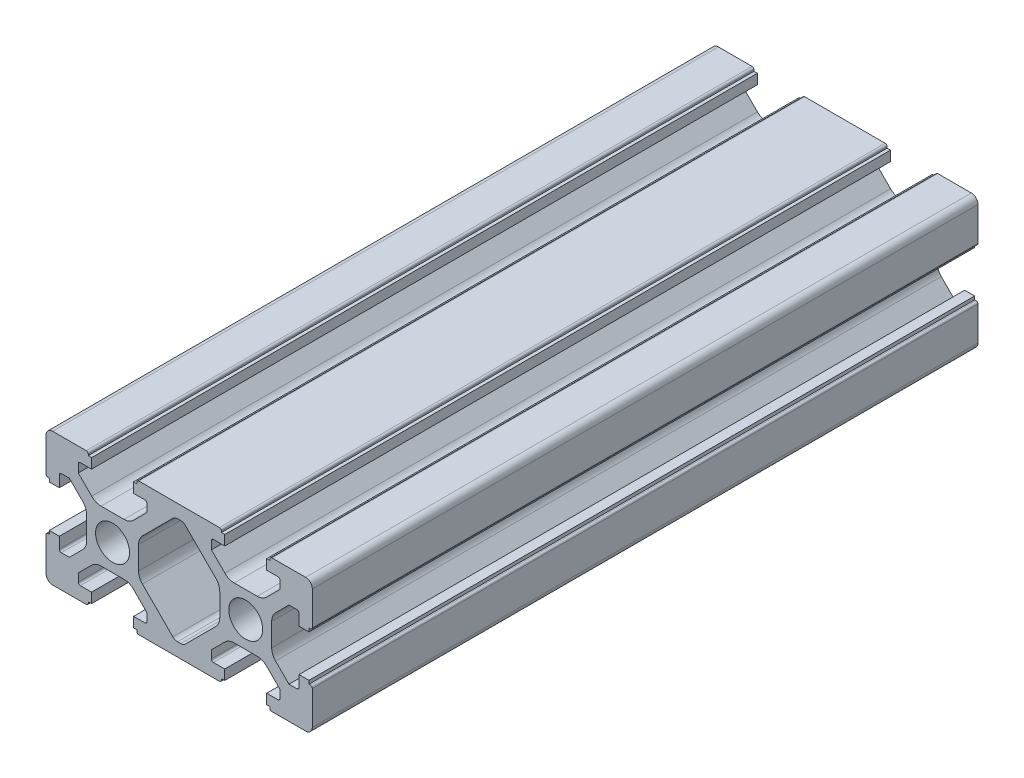
SolidWorks part; units mm, degrees
ref_plane "Front" through (0, 0, 0) normal (0, 0, 1) x (1, 0, 0)
ref_plane "Top" through (0, 0, 0) normal (0, 1, 0) x (1, 0, 0)
ref_plane "Right" through (0, 0, 0) normal (1, 0, 0) x (0, 0, -1)
sketch "草图1" plane through (0, 0, 0) normal (0, 0, 1) x (1, 0, 0)
  line L0 (-23.1654, -6.3888) -> (-23.1654, -1.3388)
  line L1 (-22.8654, -1.0388) -> (-22.6654, -1.0388)
  line L2 (-22.6654, -1.0388) -> (-22.6654, -0.5388)
  line L3 (-22.6654, -0.5388) -> (-21.1654, -0.5388)
  line L4 (-21.1654, -0.5388) -> (-21.1654, -2.2388)
  line L5 (-17.0654, 0.8896) -> (-17.0654, 4.3328)
  line L6 (-21.1654, 5.7612) -> (-21.1654, 7.4612)
  line L7 (-22.6654, 5.7612) -> (-21.1654, 5.7612)
  line L8 (-22.6654, 6.2612) -> (-22.6654, 5.7612)
  line L9 (-22.8654, 6.2612) -> (-22.6654, 6.2612)
  line L10 (-23.1654, 11.6112) -> (-23.1654, 6.5612)
  line L11 (-20.8654, 7.7612) -> (-19.6654, 7.7612)
  line L12 (-19.6654, 7.7612) -> (-17.6512, 5.747)
  line L13 (-19.6654, -2.5388) -> (-17.6512, -0.5246)
  line L14 (-20.8654, -2.5388) -> (-19.6654, -2.5388)
  line L15 (-8.0154, 10.3112) -> (-8.0154, 9.1112)
  line L16 (-8.0154, 9.1112) -> (-10.0296, 7.097)
  line L17 (-18.3154, 9.1112) -> (-16.3012, 7.097)
  line L18 (-18.3154, 10.3112) -> (-18.3154, 9.1112)
  line L19 (-22.1654, 12.6112) -> (-17.1154, 12.6112)
  line L20 (-16.8154, 12.3112) -> (-16.8154, 12.1112)
  line L21 (-16.8154, 12.1112) -> (-16.3154, 12.1112)
  line L22 (-16.3154, 12.1112) -> (-16.3154, 10.6112)
  line L23 (-16.3154, 10.6112) -> (-18.0154, 10.6112)
  line L24 (-11.4438, 6.5112) -> (-14.887, 6.5112)
  line L25 (-10.0154, 10.6112) -> (-8.3154, 10.6112)
  line L26 (-10.0154, 12.1112) -> (-10.0154, 10.6112)
  line L27 (-9.5154, 12.1112) -> (-10.0154, 12.1112)
  line L28 (-9.5154, 12.3112) -> (-9.5154, 12.1112)
  line L29 (-9.2654, 4.3328) -> (-9.2654, 0.8896)
  line L30 (-6.6654, 7.7612) -> (-8.6796, 5.747)
  line L31 (-18.3154, -5.0888) -> (-18.3154, -3.8888)
  line L32 (-18.3154, -3.8888) -> (-16.3012, -1.8746)
  line L33 (-8.0154, -3.8888) -> (-10.0296, -1.8746)
  line L34 (-8.0154, -5.0888) -> (-8.0154, -3.8888)
  line L35 (-3.1654, -7.3888) -> (-9.2154, -7.3888)
  line L36 (-9.5154, -7.0888) -> (-9.5154, -6.8888)
  line L37 (-9.5154, -6.8888) -> (-10.0154, -6.8888)
  line L38 (-10.0154, -6.8888) -> (-10.0154, -5.3888)
  line L39 (-10.0154, -5.3888) -> (-8.3154, -5.3888)
  line L40 (-14.887, -1.2888) -> (-11.4438, -1.2888)
  line L41 (-16.3154, -5.3888) -> (-18.0154, -5.3888)
  line L42 (-16.3154, -6.8888) -> (-16.3154, -5.3888)
  line L43 (-16.8154, -6.8888) -> (-16.3154, -6.8888)
  line L44 (-16.8154, -7.0888) -> (-16.8154, -6.8888)
  line L45 (-22.1654, -7.3888) -> (-17.1154, -7.3888)
  line L46 (2.9346, 0.8896) -> (2.9346, 4.3328)
  line L47 (0.3346, 7.7612) -> (2.3488, 5.747)
  line L48 (11.9846, 10.3112) -> (11.9846, 9.1112)
  line L49 (11.9846, 9.1112) -> (9.9704, 7.097)
  line L50 (1.6846, 9.1112) -> (3.6988, 7.097)
  line L51 (1.6846, 10.3112) -> (1.6846, 9.1112)
  line L52 (3.1846, 12.3112) -> (3.1846, 12.1112)
  line L53 (3.1846, 12.1112) -> (3.6846, 12.1112)
  line L54 (3.6846, 12.1112) -> (3.6846, 10.6112)
  line L55 (3.6846, 10.6112) -> (1.9846, 10.6112)
  line L56 (8.5562, 6.5112) -> (5.113, 6.5112)
  line L57 (9.9846, 10.6112) -> (11.6846, 10.6112)
  line L58 (9.9846, 12.1112) -> (9.9846, 10.6112)
  line L59 (10.4846, 12.1112) -> (9.9846, 12.1112)
  line L60 (10.4846, 12.3112) -> (10.4846, 12.1112)
  line L61 (15.8346, 12.6112) -> (10.7846, 12.6112)
  line L62 (16.8346, 11.6112) -> (16.8346, 6.5612)
  line L63 (16.5346, 6.2612) -> (16.3346, 6.2612)
  line L64 (16.3346, 6.2612) -> (16.3346, 5.7612)
  line L65 (16.3346, 5.7612) -> (14.8346, 5.7612)
  line L66 (14.8346, 5.7612) -> (14.8346, 7.4612)
  line L67 (10.7346, 4.3328) -> (10.7346, 0.8896)
  line L68 (14.8346, -0.5388) -> (14.8346, -2.2388)
  line L69 (16.3346, -0.5388) -> (14.8346, -0.5388)
  line L70 (16.3346, -1.0388) -> (16.3346, -0.5388)
  line L71 (16.5346, -1.0388) -> (16.3346, -1.0388)
  line L72 (16.8346, -6.3888) -> (16.8346, -1.3388)
  line L73 (14.5346, -2.5388) -> (13.3346, -2.5388)
  line L74 (13.3346, -2.5388) -> (11.3204, -0.5246)
  line L75 (13.3346, 7.7612) -> (11.3204, 5.747)
  line L76 (14.5346, 7.7612) -> (13.3346, 7.7612)
  line L77 (1.6846, -5.0888) -> (1.6846, -3.8888)
  line L78 (1.6846, -3.8888) -> (3.6988, -1.8746)
  line L79 (11.9846, -3.8888) -> (9.9704, -1.8746)
  line L80 (11.9846, -5.0888) -> (11.9846, -3.8888)
  line L81 (15.8346, -7.3888) -> (10.4846, -7.3888)
  line L82 (10.4846, -7.3888) -> (10.4846, -6.8888)
  line L83 (10.4846, -6.8888) -> (9.9846, -6.8888)
  line L84 (9.9846, -6.8888) -> (9.9846, -5.3888)
  line L85 (9.9846, -5.3888) -> (11.6846, -5.3888)
  line L86 (5.113, -1.2888) -> (8.5562, -1.2888)
  line L87 (3.6846, -5.3888) -> (1.9846, -5.3888)
  line L88 (3.6846, -6.8888) -> (3.6846, -5.3888)
  line L89 (3.1846, -6.8888) -> (3.6846, -6.8888)
  line L90 (3.1846, -7.0888) -> (3.1846, -6.8888)
  line L91 (-3.1654, -7.3888) -> (2.8846, -7.3888)
  line L92 (-6.6654, 7.7612) -> (-4.1083, 10.3183)
  line L93 (0.3346, 7.7612) -> (-2.2225, 10.3183)
  line L94 (-3.4012, 10.6112) -> (-2.9296, 10.6112)
  line L95 (-9.2154, 12.6112) -> (2.8846, 12.6112)
  line L96 (-3.4012, -5.3888) -> (-2.9296, -5.3888)
  line L97 (0.3346, -2.5388) -> (-2.2225, -5.0959)
  line L98 (-6.6654, -2.5388) -> (-4.1083, -5.0959)
  line L99 (-6.6654, -2.5388) -> (-8.6796, -0.5246)
  line L100 (0.3346, -2.5388) -> (2.3488, -0.5246)
  arc A0 (-8.3154, -5.3888) -> (-8.0154, -5.0888) centre (-8.3154, -5.0888) ccw
  arc A1 (-18.3154, -5.0888) -> (-18.0154, -5.3888) centre (-18.0154, -5.0888) ccw
  arc A2 (-21.1654, -2.2388) -> (-20.8654, -2.5388) centre (-20.8654, -2.2388) ccw
  arc A3 (-20.8654, 7.7612) -> (-21.1654, 7.4612) centre (-20.8654, 7.4612) ccw
  arc A4 (-18.0154, 10.6112) -> (-18.3154, 10.3112) centre (-18.0154, 10.3112) ccw
  arc A5 (-8.0154, 10.3112) -> (-8.3154, 10.6112) centre (-8.3154, 10.3112) ccw
  arc A6 (-22.8654, -1.0388) -> (-23.1654, -1.3388) centre (-22.8654, -1.3388) ccw
  arc A7 (-23.1654, 6.5612) -> (-22.8654, 6.2612) centre (-22.8654, 6.5612) ccw
  arc A8 (-23.1654, -6.3888) -> (-22.1654, -7.3888) centre (-22.1654, -6.3888) ccw
  arc A9 (-22.1654, 12.6112) -> (-23.1654, 11.6112) centre (-22.1654, 11.6112) ccw
  circle A10 centre (-13.1654, 2.6112) radius 2.55
  arc A11 (-17.0654, 4.3328) -> (-17.6512, 5.747) centre (-19.0654, 4.3328) ccw
  arc A12 (-17.6512, -0.5246) -> (-17.0654, 0.8896) centre (-19.0654, 0.8896) ccw
  arc A13 (-11.4438, 6.5112) -> (-10.0296, 7.097) centre (-11.4438, 8.5112) ccw
  arc A14 (-16.3012, 7.097) -> (-14.887, 6.5112) centre (-14.887, 8.5112) ccw
  arc A15 (-9.2654, 0.8896) -> (-8.6796, -0.5246) centre (-7.2654, 0.8896) ccw
  arc A16 (-8.6796, 5.747) -> (-9.2654, 4.3328) centre (-7.2654, 4.3328) ccw
  arc A17 (-14.887, -1.2888) -> (-16.3012, -1.8746) centre (-14.887, -3.2888) ccw
  arc A18 (-10.0296, -1.8746) -> (-11.4438, -1.2888) centre (-11.4438, -3.2888) ccw
  arc A19 (14.5346, -2.5388) -> (14.8346, -2.2388) centre (14.5346, -2.2388) ccw
  arc A20 (11.6846, -5.3888) -> (11.9846, -5.0888) centre (11.6846, -5.0888) ccw
  arc A21 (1.6846, -5.0888) -> (1.9846, -5.3888) centre (1.9846, -5.0888) ccw
  arc A22 (1.9846, 10.6112) -> (1.6846, 10.3112) centre (1.9846, 10.3112) ccw
  arc A23 (11.9846, 10.3112) -> (11.6846, 10.6112) centre (11.6846, 10.3112) ccw
  arc A24 (14.8346, 7.4612) -> (14.5346, 7.7612) centre (14.5346, 7.4612) ccw
  arc A25 (16.8346, -1.3388) -> (16.5346, -1.0388) centre (16.5346, -1.3388) ccw
  arc A26 (16.5346, 6.2612) -> (16.8346, 6.5612) centre (16.5346, 6.5612) ccw
  arc A27 (15.8346, -7.3888) -> (16.8346, -6.3888) centre (15.8346, -6.3888) ccw
  arc A28 (16.8346, 11.6112) -> (15.8346, 12.6112) centre (15.8346, 11.6112) ccw
  circle A29 centre (6.8346, 2.6112) radius 2.55
  arc A30 (2.9346, 4.3328) -> (2.3488, 5.747) centre (0.9346, 4.3328) ccw
  arc A31 (2.3488, -0.5246) -> (2.9346, 0.8896) centre (0.9346, 0.8896) ccw
  arc A32 (8.5562, 6.5112) -> (9.9704, 7.097) centre (8.5562, 8.5112) ccw
  arc A33 (3.6988, 7.097) -> (5.113, 6.5112) centre (5.113, 8.5112) ccw
  arc A34 (10.7346, 0.8896) -> (11.3204, -0.5246) centre (12.7346, 0.8896) ccw
  arc A35 (11.3204, 5.747) -> (10.7346, 4.3328) centre (12.7346, 4.3328) ccw
  arc A36 (5.113, -1.2888) -> (3.6988, -1.8746) centre (5.113, -3.2888) ccw
  arc A37 (9.9704, -1.8746) -> (8.5562, -1.2888) centre (8.5562, -3.2888) ccw
  arc A38 (-3.4012, 10.6112) -> (-4.1083, 10.3183) centre (-3.4012, 9.6112) ccw
  arc A39 (-2.2225, 10.3183) -> (-2.9296, 10.6112) centre (-2.9296, 9.6112) ccw
  arc A40 (-2.9296, -5.3888) -> (-2.2225, -5.0959) centre (-2.9296, -4.3888) ccw
  arc A41 (-4.1083, -5.0959) -> (-3.4012, -5.3888) centre (-3.4012, -4.3888) ccw
  arc A42 (2.8846, -7.3888) -> (3.1846, -7.0888) centre (2.8846, -7.0888) ccw
  arc A43 (-9.5154, -7.0888) -> (-9.2154, -7.3888) centre (-9.2154, -7.0888) ccw
  arc A44 (-17.1154, -7.3888) -> (-16.8154, -7.0888) centre (-17.1154, -7.0888) ccw
  arc A45 (10.7846, 12.6112) -> (10.4846, 12.3112) centre (10.7846, 12.3112) ccw
  arc A46 (3.1846, 12.3112) -> (2.8846, 12.6112) centre (2.8846, 12.3112) ccw
  arc A47 (-9.2154, 12.6112) -> (-9.5154, 12.3112) centre (-9.2154, 12.3112) ccw
  arc A48 (-16.8154, 12.3112) -> (-17.1154, 12.6112) centre (-17.1154, 12.3112) ccw
  point P199 (-23.1654, 9.0862)
  dimension "D1" = 20
  dimension "D2" = 40
extrude "凸台-拉伸1" add sketch "草图1" along normal blind 100
